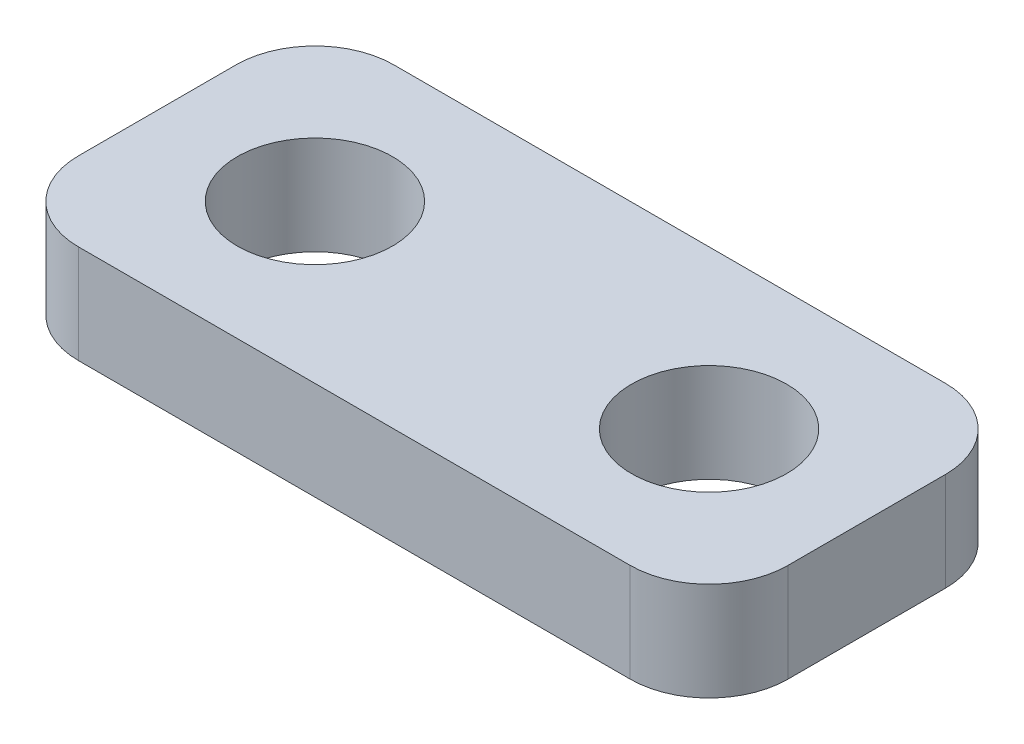
SolidWorks part; units mm, degrees
ref_plane "Front Plane" through (0, 0, 0) normal (0, 0, 1) x (1, 0, 0)
ref_plane "Top Plane" through (0, 0, 0) normal (0, 1, 0) x (1, 0, 0)
ref_plane "Right Plane" through (0, 0, 0) normal (1, 0, 0) x (0, 0, -1)
sketch "Sketch1" plane through (0, 0, 0) normal (0, 1, 0) x (1, 0, 0)
  line L1 (-11.43, -5.08) -> (11.43, -5.08)
  line L2 (-11.43, -5.08) -> (-11.43, 5.08)
  line L3 (-11.43, 5.08) -> (11.43, 5.08)
  line L4 (11.43, -5.08) -> (11.43, 5.08)
  line L5 (-11.43, -5.08) -> (11.43, 5.08) construction
  line L6 (-11.43, 5.08) -> (11.43, -5.08) construction
  point P0 (0, 0)
  dimension "D1" = 10.16
  dimension "D2" = 22.86
extrude "Boss-Extrude1" add sketch "Sketch1" along normal blind 3.175
sketch "Sketch2" plane through (0, 3.175, 0) normal (0, 1, 0) x (1, 0, 0)
  line L0 (11.43, 5.08) -> (-11.43, 5.08) construction
  line L1 (-11.43, 5.08) -> (-11.43, -5.08) construction
  line L2 (0, -5.08) -> (0, 5.08) construction
  line L3 (-11.43, -5.08) -> (11.43, -5.08) construction
  line L4 (-11.43, 0) -> (11.43, 0) construction
  line L5 (11.43, -5.08) -> (11.43, 5.08) construction
  circle A0 centre (-6.35, 0) radius 2.5
  circle A3 centre (6.35, 0) radius 2.5
  point P2 (-8.85, 0)
  point P3 (-6.35, 2.5)
  dimension "D1" = 5
  dimension "D2" = 12.7
extrude "Cut-Extrude1" cut sketch "Sketch2" against normal through all
sketch "Sketch3" plane through (0, 3.175, 0) normal (0, 1, 0) x (1, 0, 0)
  line L0 (-8.85, 0) -> (-8.85, 5.08)
  line L5 (-11.43, 5.08) -> (11.43, 5.08) construction
  line L6 (-8.85, 5.08) -> (-4.5845, 5.08)
  line L7 (-4.5845, 5.08) -> (-4.5845, 1.7701)
  circle A0 centre (-6.35, 0) radius 2.5 construction
  arc A1 (-4.5845, 1.7701) -> (-8.85, 0) centre (-6.35, 0) ccw
  dimension "D1" = 5.08
  dimension "D2" = 3.3099
fillet "Fillet1" radius 2.54 4 edges at (11.43, 1.5875, 5.08) (-11.43, 1.5875, 5.08) (-11.43, 1.5875, -5.08) (11.43, 1.5875, -5.08)
